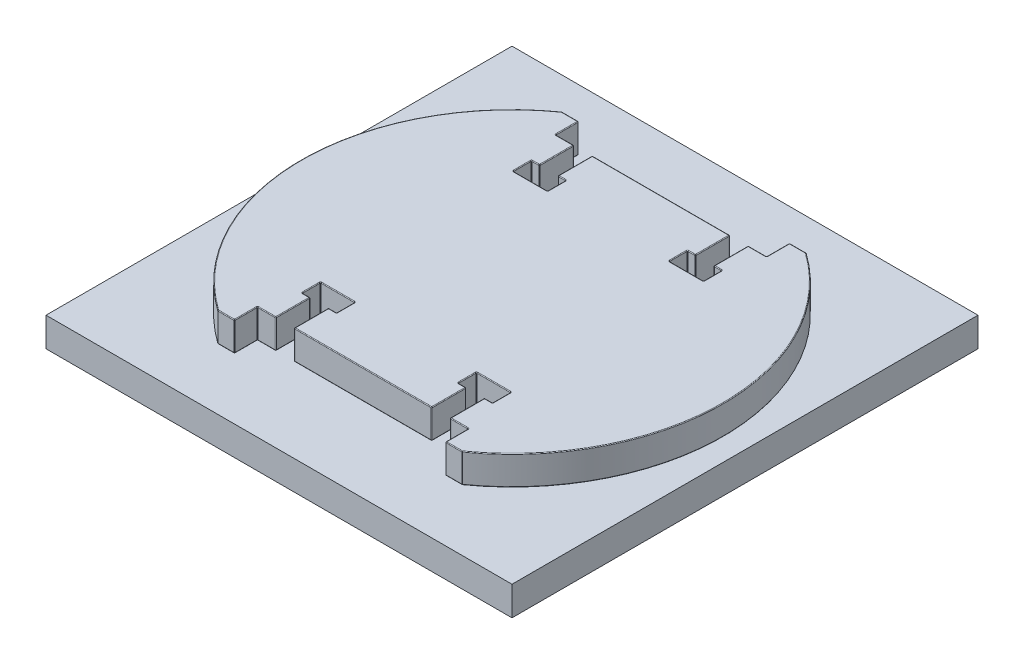
SolidWorks part; units mm, degrees
ref_plane "Front Plane" through (0, 0, 0) normal (0, 0, 1) x (1, 0, 0)
ref_plane "Top Plane" through (0, 0, 0) normal (0, 1, 0) x (1, 0, 0)
ref_plane "Right Plane" through (0, 0, 0) normal (1, 0, 0) x (0, 0, -1)
sketch "Sketch1" plane through (0, 0, 0) normal (0, 1, 0) x (1, 0, 0)
  line L0 (-26.6411, 37.5) -> (-23, 37.5)
  line L1 (23, 37.5) -> (26.6411, 37.5)
  line L3 (-23, 37.5) -> (-23, 32.5)
  line L4 (-23, 32.5) -> (23, 32.5)
  line L5 (23, 37.5) -> (23, 32.5)
  line L6 (0, 0) -> (-46, 0) construction
  line L7 (23, -37.5) -> (26.6411, -37.5)
  line L8 (23, -37.5) -> (23, -32.5)
  line L9 (-23, -32.5) -> (23, -32.5)
  line L10 (-23, -37.5) -> (-23, -32.5)
  line L11 (-26.6411, -37.5) -> (-23, -37.5)
  arc A0 (-26.6411, 37.5) -> (-26.6411, -37.5) centre (0, 0) ccw
  arc A1 (26.6411, -37.5) -> (26.6411, 37.5) centre (0, 0) ccw
  point P10 (0, 32.5)
  dimension "D1" = 92
  dimension "D2" = 37.5
  dimension "D3" = 46
  dimension "D4" = 5
extrude "Boss-Extrude1" add sketch "Sketch1" along normal blind 6.35
sketch "Sketch2" plane through (0, 6.35, 0) normal (0, 1, 0) x (1, 0, 0)
  line L0 (23, 32.5) -> (-23, 32.5) construction
  line L1 (-19, 25) -> (-15, 25)
  line L2 (-19, 25) -> (-19, 32.5)
  line L3 (-19, 32.5) -> (-15, 32.5)
  line L4 (-15, 25) -> (-15, 32.5)
  line L5 (-19, 25) -> (-15, 32.5) construction
  line L6 (-19, 32.5) -> (-15, 25) construction
  line L7 (-23, 32.5) -> (-23, 37.5) construction
  line L8 (-13.25, 21) -> (-20.75, 21)
  line L9 (-13.25, 21) -> (-13.25, 25)
  line L10 (-13.25, 25) -> (-20.75, 25)
  line L11 (-20.75, 21) -> (-20.75, 25)
  line L12 (-13.25, 21) -> (-20.75, 25) construction
  line L13 (-13.25, 25) -> (-20.75, 21) construction
  line L14 (0, 0) -> (-46, 0) construction
  line L15 (0, 0) -> (0, 32.5) construction
  line L16 (13.25, 25) -> (20.75, 21) construction
  line L17 (13.25, 21) -> (20.75, 25) construction
  line L18 (19, 32.5) -> (15, 25) construction
  line L19 (19, 25) -> (15, 32.5) construction
  line L20 (20.75, 21) -> (20.75, 25)
  line L21 (13.25, 25) -> (20.75, 25)
  line L22 (13.25, 21) -> (13.25, 25)
  line L23 (13.25, 21) -> (20.75, 21)
  line L24 (15, 25) -> (15, 32.5)
  line L25 (19, 32.5) -> (15, 32.5)
  line L26 (19, 25) -> (19, 32.5)
  line L27 (19, 25) -> (15, 25)
  line L28 (19, -25) -> (15, -32.5) construction
  line L29 (19, -32.5) -> (15, -25) construction
  line L30 (13.25, -21) -> (20.75, -25) construction
  line L31 (13.25, -25) -> (20.75, -21) construction
  line L32 (-13.25, -25) -> (-20.75, -21) construction
  line L33 (-13.25, -21) -> (-20.75, -25) construction
  line L34 (-19, -32.5) -> (-15, -25) construction
  line L35 (-19, -25) -> (-15, -32.5) construction
  line L36 (19, -25) -> (15, -25)
  line L37 (19, -25) -> (19, -32.5)
  line L38 (19, -32.5) -> (15, -32.5)
  line L39 (15, -25) -> (15, -32.5)
  line L40 (13.25, -21) -> (20.75, -21)
  line L41 (13.25, -21) -> (13.25, -25)
  line L42 (13.25, -25) -> (20.75, -25)
  line L43 (20.75, -21) -> (20.75, -25)
  line L44 (-20.75, -21) -> (-20.75, -25)
  line L45 (-13.25, -25) -> (-20.75, -25)
  line L46 (-13.25, -21) -> (-13.25, -25)
  line L47 (-13.25, -21) -> (-20.75, -21)
  line L48 (-15, -25) -> (-15, -32.5)
  line L49 (-19, -32.5) -> (-15, -32.5)
  line L50 (-19, -25) -> (-19, -32.5)
  line L51 (-19, -25) -> (-15, -25)
  arc A0 (-26.6411, 37.5) -> (-26.6411, -37.5) centre (0, 0) ccw construction
  point P0 (-17, 28.75)
  point P7 (-17, 23)
  point P29 (17, 23)
  point P30 (17, 28.75)
  point P47 (17, -28.75)
  point P48 (17, -23)
  point P49 (-17, -23)
  point P50 (-17, -28.75)
  dimension "D1" = 4
  dimension "D2" = 4
  dimension "D3" = 7.5
  dimension "D4" = 4
  dimension "D5" = 7.5
extrude "Cut-Extrude1" cut sketch "Sketch2" against normal through all contours L4 L3 L2 L1 | L9 L10 L11 L8 | L26 L25 L24 L27 | L20 L21 L22 L23 | L43 L42 L41 L40 | L37 L38 L39 L36 | L48 L49 L50 L51 | L46 L45 L44 L47
fillet "Fillet1" radius 0.15 132 edges at (-19, 3.175, -32.5) (-19, 6.35, -28.75) (-21, 6.35, -32.5) (-19, 0, -28.75) (-19, 3.175, -25) (-23, 3.175, -32.5) (-21, 0, -32.5) (-19.875, 6.35, -25) (-23, 6.35, -35) (-19.875, 0, -25) (-20.75, 3.175, -25) (-23, 3.175, -37.5) (-23, 0, -35) (-20.75, 6.35, -23) (-24.8206, 6.35, -37.5) (-20.75, 0, -23) (-20.75, 3.175, -21) (-26.6411, 3.175, -37.5) (-24.8206, 0, -37.5) (-17, 6.35, -21) (-46, 6.35, 0) (-17, 0, -21) (-13.25, 3.175, -21) (-26.6411, 3.175, 37.5) (-46, 0, 0) (-13.25, 6.35, -23) (-24.8206, 6.35, 37.5) (-13.25, 0, -23) (-13.25, 3.175, -25) (-23, 3.175, 37.5) (-24.8206, 0, 37.5) (-14.125, 6.35, -25) (-23, 6.35, 35) (-14.125, 0, -25) (-15, 3.175, -25) (-23, 3.175, 32.5) (-23, 0, 35) (-15, 6.35, -28.75) (-21, 6.35, 32.5) (-15, 0, -28.75) (-15, 3.175, -32.5) (-21, 0, 32.5) (-19, 3.175, 32.5) (0, 6.35, -32.5) (-19, 6.35, 28.75) (0, 0, -32.5) (15, 3.175, -32.5) (-19, 0, 28.75) (-19, 3.175, 25) (15, 6.35, -28.75) (-19.875, 6.35, 25) (15, 0, -28.75) (15, 3.175, -25) (-20.75, 3.175, 25) (-19.875, 0, 25) (14.125, 6.35, -25) (-20.75, 6.35, 23) (14.125, 0, -25) (13.25, 3.175, -25) (-20.75, 0, 23) (-20.75, 3.175, 21) (13.25, 6.35, -23) (-17, 6.35, 21) (13.25, 0, -23) (13.25, 3.175, -21) (-17, 0, 21) (-13.25, 3.175, 21) (17, 6.35, -21) (-13.25, 6.35, 23) (17, 0, -21) (20.75, 3.175, -21) (-13.25, 0, 23) (-13.25, 3.175, 25) (20.75, 6.35, -23) (-14.125, 6.35, 25) (20.75, 0, -23) (20.75, 3.175, -25) (-14.125, 0, 25) (-15, 3.175, 25) (19.875, 6.35, -25) (-15, 6.35, 28.75) (19.875, 0, -25) (19, 3.175, -25) (-15, 3.175, 32.5) (-15, 0, 28.75) (19, 6.35, -28.75) (0, 6.35, 32.5) (19, 0, -28.75) (19, 3.175, -32.5) (0, 0, 32.5) (15, 3.175, 32.5) (21, 6.35, -32.5) (15, 6.35, 28.75) (21, 0, -32.5) (23, 3.175, -32.5) (15, 0, 28.75) (15, 3.175, 25) (23, 6.35, -35) (14.125, 6.35, 25) (23, 0, -35) (23, 3.175, -37.5) (14.125, 0, 25) (13.25, 3.175, 25) (24.8206, 6.35, -37.5) (13.25, 6.35, 23) (24.8206, 0, -37.5) (26.6411, 3.175, -37.5) (13.25, 0, 23) (13.25, 3.175, 21) (46, 6.35, 0) (17, 6.35, 21) (46, 0, 0) (26.6411, 3.175, 37.5) (20.75, 3.175, 21) (17, 0, 21) (24.8206, 6.35, 37.5) (20.75, 6.35, 23) (23, 3.175, 37.5) (24.8206, 0, 37.5) (20.75, 3.175, 25) (20.75, 0, 23) (23, 6.35, 35) (19.875, 6.35, 25) (23, 0, 35) (23, 3.175, 32.5) (19, 3.175, 25) (19.875, 0, 25) (21, 6.35, 32.5) (19, 6.35, 28.75) (21, 0, 32.5) (19, 0, 28.75) (19, 3.175, 32.5)
sketch "Sketch3" plane through (0, 0, 0) normal (0, -1, 0) x (1, 0, 0)
  line L1 (-50.8, 50.8) -> (50.8, 50.8)
  line L2 (-50.8, 50.8) -> (-50.8, -50.8)
  line L3 (-50.8, -50.8) -> (50.8, -50.8)
  line L4 (50.8, 50.8) -> (50.8, -50.8)
  line L5 (-50.8, 50.8) -> (50.8, -50.8) construction
  line L6 (-50.8, -50.8) -> (50.8, 50.8) construction
  point P0 (0, 0)
  dimension "D1" = 101.6
  dimension "D2" = 101.6
extrude "Boss-Extrude2" add sketch "Sketch3" along normal blind 6.35
